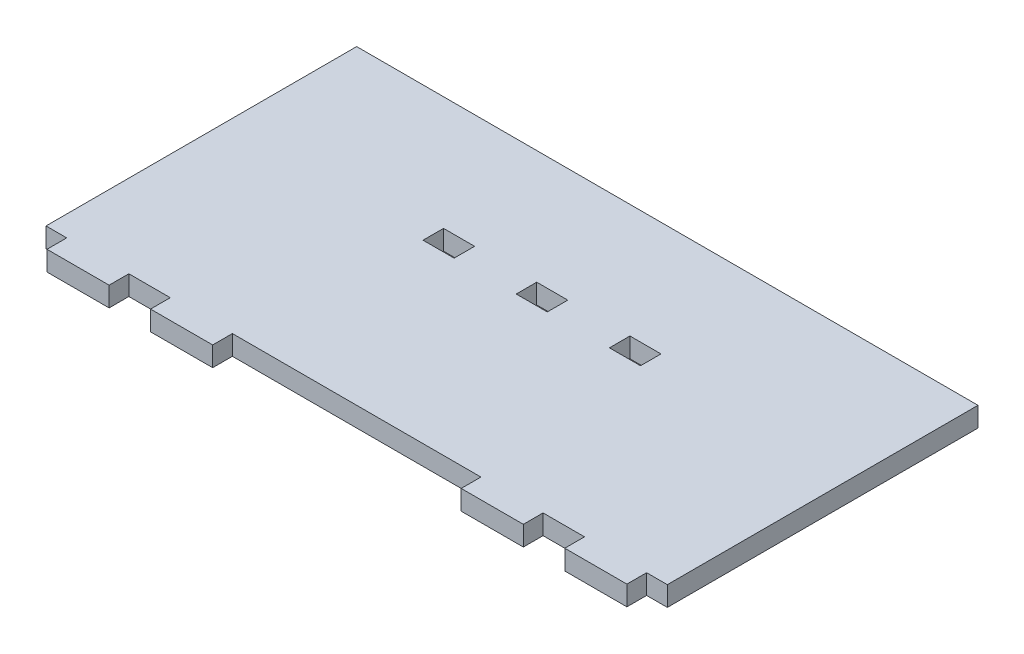
SolidWorks part; units mm, degrees
ref_plane "Front Plane" through (0, 0, 0) normal (0, 0, 1) x (1, 0, 0)
ref_plane "Top Plane" through (0, 0, 0) normal (0, 1, 0) x (1, 0, 0)
ref_plane "Right Plane" through (0, 0, 0) normal (1, 0, 0) x (0, 0, -1)
sketch "Sketch1" plane through (0, 0, 0) normal (0, 1, 0) x (1, 0, 0)
  line L0 (0, 25) -> (0, -25) construction
  line L1 (-50, 25) -> (50, 25)
  line L2 (-50, 25) -> (-50, -25)
  line L3 (-50, -25) -> (-46.6667, -25)
  line L4 (50, 25) -> (50, -25)
  line L5 (-50, 25) -> (50, -25) construction
  line L6 (-50, -25) -> (50, 25) construction
  line L8 (-46.6667, -25) -> (-46.6667, -28.175)
  line L9 (-46.6667, -28.175) -> (-36.6667, -28.175)
  line L10 (-36.6667, -25) -> (-36.6667, -28.175)
  line L12 (-30, -25) -> (-30, -28.175)
  line L13 (-30, -28.175) -> (-20, -28.175)
  line L14 (-20, -25) -> (-20, -28.175)
  line L15 (30, -28.175) -> (20, -28.175)
  line L16 (20, -25) -> (20, -28.175)
  line L18 (30, -25) -> (30, -28.175)
  line L19 (46.6667, -28.175) -> (36.6667, -28.175)
  line L20 (36.6667, -25) -> (36.6667, -28.175)
  line L22 (46.6667, -25) -> (46.6667, -28.175)
  line L23 (-36.6667, -25) -> (-30, -25)
  line L24 (-20, -25) -> (20, -25)
  line L25 (30, -25) -> (36.6667, -25)
  line L26 (46.6667, -25) -> (50, -25)
  point P0 (0, 0)
  dimension "D1" = 50
  dimension "D2" = 100
  dimension "D3" = 3.3333
  dimension "D4" = 10
  dimension "D5" = 3.175
  dimension "D6" = 3.175
  dimension "D7" = 10
  dimension "D8" = 6.6667
extrude "Boss-Extrude1" add sketch "Sketch1" along normal blind 3.175
sketch "Sketch2" plane through (0, 3.175, 0) normal (0, 1, 0) x (1, 0, 0)
  line L0 (-50, 5) -> (50, 5) construction
  line L1 (-50, 25) -> (-50, -25) construction
  line L2 (50, -25) -> (50, 25) construction
  line L4 (2.3304, 3.35) -> (-2.6696, 3.35)
  line L5 (2.3304, 3.35) -> (2.3304, 6.65)
  line L6 (2.3304, 6.65) -> (-2.6696, 6.65)
  line L7 (-2.6696, 3.35) -> (-2.6696, 6.65)
  line L8 (2.3304, 3.35) -> (-2.6696, 6.65) construction
  line L9 (2.3304, 6.65) -> (-2.6696, 3.35) construction
  line L10 (-17.6696, 3.35) -> (-12.6696, 3.35)
  line L11 (-17.6696, 3.35) -> (-17.6696, 6.65)
  line L12 (-17.6696, 6.65) -> (-12.6696, 6.65)
  line L13 (-12.6696, 3.35) -> (-12.6696, 6.65)
  line L14 (-17.6696, 3.35) -> (-12.6696, 6.65) construction
  line L15 (-17.6696, 6.65) -> (-12.6696, 3.35) construction
  line L16 (17.3304, 3.35) -> (12.3304, 3.35)
  line L17 (17.3304, 3.35) -> (17.3304, 6.65)
  line L18 (17.3304, 6.65) -> (12.3304, 6.65)
  line L19 (12.3304, 3.35) -> (12.3304, 6.65)
  line L20 (17.3304, 3.35) -> (12.3304, 6.65) construction
  line L21 (17.3304, 6.65) -> (12.3304, 3.35) construction
  point P2 (-0.1696, 5)
  point P3 (0, 0)
  point P6 (0, 0)
  point P11 (0, 0)
  point P12 (-15.1696, 5)
  point P17 (14.8304, 5)
  dimension "D1" = 3.3
  dimension "D2" = 3.3
  dimension "D3" = 3.3
  dimension "D4" = 5
  dimension "D5" = 5
  dimension "D6" = 5
  dimension "D7" = 10
  dimension "D8" = 10
  dimension "D9" = 20
extrude "Cut-Extrude1" cut sketch "Sketch2" against normal blind 3.175
